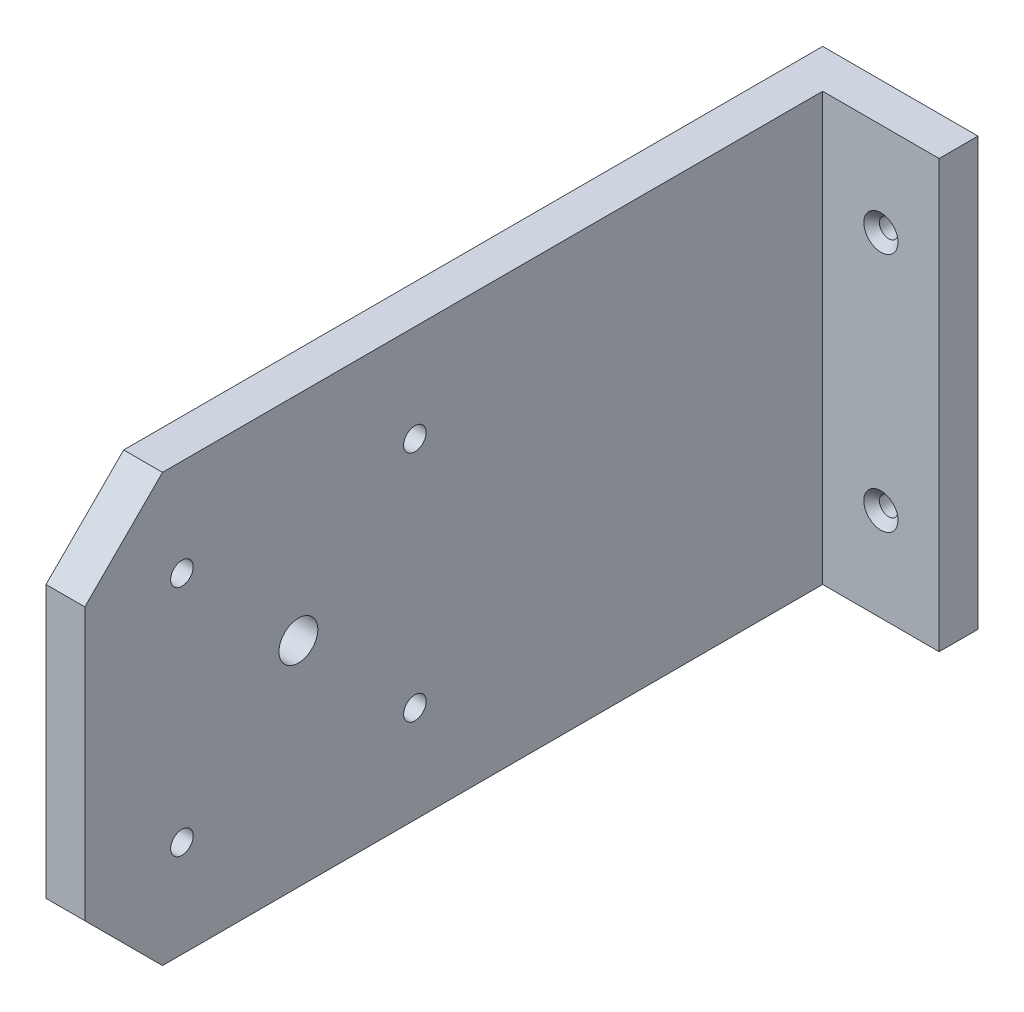
SolidWorks part; units mm, degrees
ref_plane "Ön Düzlem" through (0, 0, 0) normal (0, 0, 1) x (1, 0, 0)
ref_plane "Üst Düzlem" through (0, 0, 0) normal (0, 1, 0) x (1, 0, 0)
ref_plane "Sağ Düzlem" through (0, 0, 0) normal (1, 0, 0) x (0, 0, -1)
sketch "Sketch1" plane through (0, 0, 0) normal (1, 0, 0) x (0, 0, -1)
  line L1 (-50, 27.5) -> (50, 27.5)
  line L2 (-50, 27.5) -> (-50, -27.5)
  line L3 (-50, -27.5) -> (50, -27.5)
  line L4 (50, 27.5) -> (50, -27.5)
  line L5 (-50, 27.5) -> (50, -27.5) construction
  line L6 (-50, -27.5) -> (50, 27.5) construction
  point P0 (0, 0)
  dimension "D1" = 55
  dimension "D2" = 100
extrude "Boss-Extrude1" add sketch "Sketch1" along normal blind 5
sketch "Sketch2" plane through (5, 0, 0) normal (1, 0, 0) x (0, 0, -1)
  line L0 (-50, -27.5) -> (50, -27.5) construction
  line L1 (50, 27.5) -> (45, 27.5)
  line L2 (50, 27.5) -> (50, -27.5)
  line L3 (50, -27.5) -> (45, -27.5)
  line L4 (45, 27.5) -> (45, -27.5)
  dimension "D1" = 5
extrude "Boss-Extrude2" add sketch "Sketch2" along normal blind 15
sketch "Sketch3" plane through (0, 0, 0) normal (-1, 0, 0) x (0, 0, 1)
  line L0 (50, 27.5) -> (40, 27.5)
  line L1 (-50, 27.5) -> (50, 27.5) construction
  line L2 (40, 27.5) -> (50, 17.5)
  line L3 (50, 27.5) -> (50, -27.5) construction
  line L4 (50, 17.5) -> (50, 27.5)
  line L5 (50, -27.5) -> (40, -27.5)
  line L6 (50, -27.5) -> (-50, -27.5) construction
  line L7 (40, -27.5) -> (50, -17.5)
  line L8 (50, -17.5) -> (50, -27.5)
  dimension "D1" = 10
  dimension "D2" = 45
  dimension "D3" = 45
  dimension "D4" = 10
extrude "Cut-Extrude1" cut sketch "Sketch3" against normal up to next
hole_wizard "CSK for M2 Flat Head Machine Screw1" positions "Sketch5" profile "Sketch4" countersink size "M2" standard "ANSI Metric" end condition through all
sketch "Sketch5" plane through (0, 0, -45) normal (0, 0, 1) x (1, 0, 0)
  line L0 (20, 27.5) -> (5, 27.5) construction
  line L1 (20, -27.5) -> (5, -27.5) construction
  line L2 (5, 27.5) -> (5, -27.5) construction
  point P0 (12.5, 15.5)
  point P2 (12.5, -15.5)
  dimension "D1" = 12
  dimension "D2" = 12
  dimension "D3" = 7.5
  dimension "D4" = 7.5
sketch "Sketch4" plane through (12.5, 15.5, -45) normal (1, 0, 0) x (0, -1, 0)
  line L0 (0, 0) -> (0, 5)
  line L1 (0, 5) -> (1.2, 5)
  line L2 (1.2, 5) -> (1.2, 1)
  line L3 (1.2, 1) -> (2.2, 0)
  line L5 (2.2, 0) -> (0, 0)
  line L6 (-1.2, 1) -> (-2.2, 0) construction
  line L11 (0, -6.35) -> (0, 107.95) construction
  dimension "Thru Hole Dia." = 2.4
  dimension "Thru Hole Depth" = 5
  dimension "Near C'Sink Dia." = 4.4
  dimension "Near C'Sink Angle" = 90
sketch "Sketch6" plane through (0, 0, 0) normal (-1, 0, 0) x (0, 0, 1)
  circle A0 centre (22.5, 0) radius 2.5
extrude "Cut-Extrude2" cut sketch "Sketch6" against normal up to next
hole_wizard "CSK for M2.5 Flat Head Machine Screw1" positions "Sketch8" profile "Sketch9" countersink size "M2.5" standard "ANSI Metric" end condition up to next
sketch "Sketch8" plane through (0, 0, 0) normal (-1, 0, 0) x (0, 0, 1)
  point P0 (7.5, 15)
  point P3 (7.5, -15)
  point P6 (37.5, -15)
  point P9 (37.5, 15)
sketch "Sketch9" plane through (0, 15, 7.5) normal (0, 1, 0) x (0, 0, 1)
  line L0 (0, 0) -> (0, 5)
  line L1 (0, 5) -> (1.45, 5)
  line L2 (1.45, 5) -> (1.45, 1.3)
  line L3 (1.45, 1.3) -> (2.75, 0)
  line L5 (2.75, 0) -> (0, 0)
  line L6 (-1.45, 1.3) -> (-2.75, 0) construction
  line L11 (0, -6.35) -> (0, 107.95) construction
  dimension "Thru Hole Dia." = 2.9
  dimension "Thru Hole Depth" = 5
  dimension "Near C'Sink Dia." = 5.5
  dimension "Near C'Sink Angle" = 90
